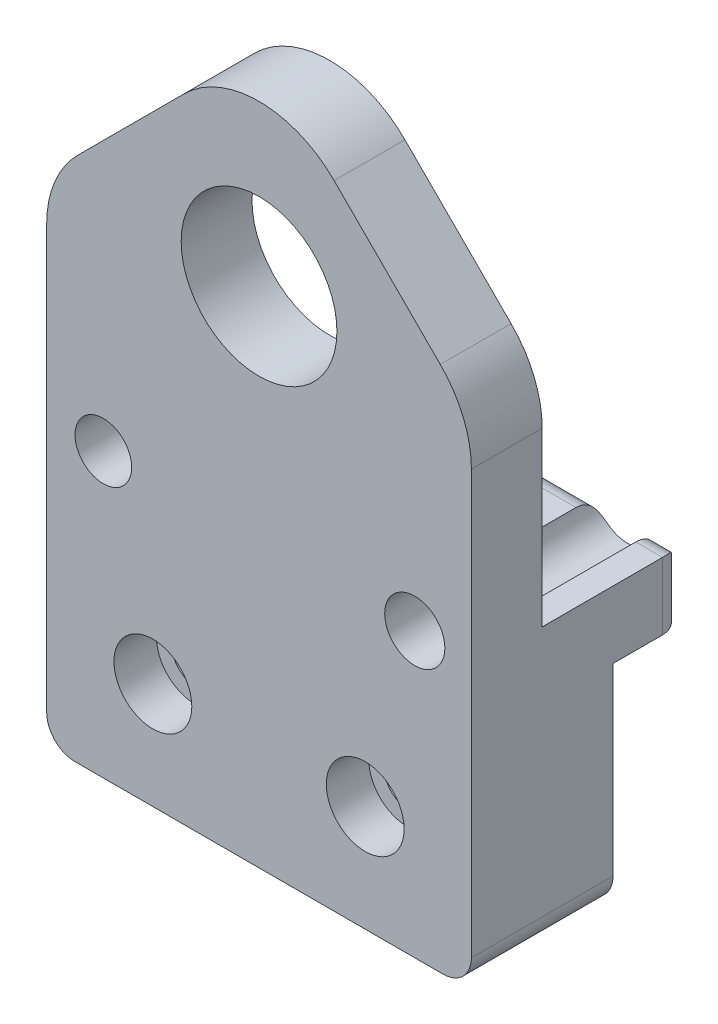
SolidWorks part; units mm, degrees
ref_plane "Front Plane" through (0, 0, 0) normal (0, 0, 1) x (1, 0, 0)
ref_plane "Top Plane" through (0, 0, 0) normal (0, 1, 0) x (1, 0, 0)
ref_plane "Right Plane" through (0, 0, 0) normal (1, 0, 0) x (0, 0, -1)
sketch "Esboço2" plane through (0, 0, 0) normal (0, 0, 1) x (1, 0, 0)
  line L0 (250, 102.2122) -> (250, 76.2122) construction
  line L1 (190, 102.2122) -> (190, 76.2122) construction
  line L2 (250, 102.2122) -> (250, 76.2122)
  line L3 (190, 102.2122) -> (190, 76.2122)
  line L4 (194, 72.2122) -> (246, 72.2122)
  line L6 (194, 172.2122) -> (246, 172.2122) construction
  line L14 (209.3934, 161.6056) -> (194.3934, 146.6056)
  line L15 (190, 76.2122) -> (190, 168.2122) construction
  line L16 (190, 135.999) -> (190, 102.2122)
  line L17 (230.6066, 161.6056) -> (245.6066, 146.6056)
  line L18 (250, 168.2122) -> (250, 76.2122) construction
  line L19 (250, 135.999) -> (250, 102.2122)
  arc A0 (190, 76.2122) -> (194, 72.2122) centre (194, 76.2122) ccw construction
  arc A1 (246, 72.2122) -> (250, 76.2122) centre (246, 76.2122) ccw construction
  arc A2 (190, 76.2122) -> (194, 72.2122) centre (194, 76.2122) ccw
  arc A3 (246, 72.2122) -> (250, 76.2122) centre (246, 76.2122) ccw
  circle A13 centre (198, 112.2122) radius 4
  circle A14 centre (198, 112.2122) radius 4
  circle A16 centre (242, 112.2122) radius 4.25
  circle A17 centre (242, 112.2122) radius 4.25
  arc A18 (209.3934, 161.6056) -> (230.6066, 161.6056) centre (220, 150.999) cw
  arc A19 (245.6066, 146.6056) -> (250, 135.999) centre (235, 135.999) cw
  circle A20 centre (220, 143.3622) radius 11
  arc A21 (194.3934, 146.6056) -> (190, 135.999) centre (205, 135.999) ccw
  point P15 (220, 172.2122)
  point P21 (220, 172.2122)
  point P29 (250, 142.2122)
  point P32 (190, 142.2122)
  dimension "D3" = 22
  dimension "D4" = 15
  dimension "D5" = 15
  dimension "D1" = 0
  dimension "D2" = 0
extrude "Ressalto-extrusão1" add sketch "Esboço2" along normal blind 20
sketch "Esboço3" plane through (0, 0, 0) normal (0, 0, -1) x (-1, 0, 0)
  line L0 (-440, 102.2122) -> (0, 102.2122) construction
  line L1 (-440, 102.2122) -> (0, 102.2122)
  line L2 (-190, 135.999) -> (-190, 76.2122) construction
  line L4 (-190, 102.2122) -> (-250, 102.2122)
  line L5 (-190, 102.2122) -> (-190, 111.6979)
  line L6 (-190, 111.6979) -> (-194.0332, 111.6979)
  line L7 (-250, 102.2122) -> (-250, 111.6979)
  line L8 (-250, 76.2122) -> (-250, 135.999) construction
  line L9 (-190, 111.6979) -> (-250, 111.6979) construction
  line L10 (-246.2188, 111.6979) -> (-250, 111.6979)
  line L11 (-201.9668, 111.6979) -> (-237.7812, 111.6979)
  circle A2 centre (-242, 112.2122) radius 4.25
  arc A3 (-246.2188, 111.6979) -> (-237.7812, 111.6979) centre (-242, 112.2122) ccw
  circle A5 centre (-198, 112.2122) radius 4
  arc A6 (-201.9668, 111.6979) -> (-194.0332, 111.6979) centre (-198, 112.2122) ccw
  line M4 (-190, 76.2122) -> (-190, 135.999)
  line M10 (-250, 135.999) -> (-250, 76.2122)
  circle M11 centre (-242, 112.2122) radius 4.25
  circle M13 centre (-198, 112.2122) radius 4
  dimension "D1" = 0
  dimension "D2" = 0
extrude "Ressalto-extrusão2" add sketch "Esboço3" along normal blind 10 contours L11 L10 L1 L6 M13 M11 M10 M4
fillet "Filete1" radius 3 5 edges at (192.0166, 111.6979, -10) (248.1094, 111.6979, -10) (219.874, 111.6979, -10) (250, 106.955, -10) (190, 106.955, -10)
sketch "Esboço4" plane through (0, 0, 0) normal (0, 0, -1) x (-1, 0, 0)
  line L14 (-194.0332, 111.6979) -> (-190, 111.6979)
  line L15 (-190, 111.6979) -> (-190, 135.999)
  line L16 (-194.3934, 146.6056) -> (-209.3934, 161.6056)
  line L17 (-230.6066, 161.6056) -> (-245.6066, 146.6056)
  line L18 (-250, 135.999) -> (-250, 111.6979)
  line L19 (-250, 111.6979) -> (-246.2188, 111.6979)
  line L20 (-237.7812, 111.6979) -> (-201.9668, 111.6979)
  line L21 (-194.0332, 111.6979) -> (-190, 111.6979)
  line L22 (-190, 111.6979) -> (-190, 135.999)
  line L23 (-194.3934, 146.6056) -> (-209.3934, 161.6056)
  line L24 (-230.6066, 161.6056) -> (-245.6066, 146.6056)
  line L25 (-250, 135.999) -> (-250, 111.6979)
  line L26 (-250, 111.6979) -> (-246.2188, 111.6979)
  line L27 (-237.7812, 111.6979) -> (-201.9668, 111.6979)
  arc A10 (-190, 135.999) -> (-194.3934, 146.6056) centre (-205, 135.999) ccw
  arc A11 (-209.3934, 161.6056) -> (-230.6066, 161.6056) centre (-220, 150.999) ccw
  arc A12 (-245.6066, 146.6056) -> (-250, 135.999) centre (-235, 135.999) ccw
  arc A13 (-237.7812, 111.6979) -> (-246.2188, 111.6979) centre (-242, 112.2122) ccw
  arc A14 (-194.0332, 111.6979) -> (-201.9668, 111.6979) centre (-198, 112.2122) ccw
  arc A15 (-190, 135.999) -> (-194.3934, 146.6056) centre (-205, 135.999) ccw
  arc A16 (-209.3934, 161.6056) -> (-230.6066, 161.6056) centre (-220, 150.999) ccw
  arc A17 (-245.6066, 146.6056) -> (-250, 135.999) centre (-235, 135.999) ccw
  arc A18 (-237.7812, 111.6979) -> (-246.2188, 111.6979) centre (-242, 112.2122) ccw
  arc A19 (-194.0332, 111.6979) -> (-201.9668, 111.6979) centre (-198, 112.2122) ccw
  dimension "D1" = 0
extrude "Corte-extrusão1" cut sketch "Esboço4" against normal blind 10
sketch "Esboço7" plane through (0, 0, 20) normal (0, 0, 1) x (1, 0, 0)
  circle A2 centre (235, 87.2122) radius 5.5
  circle A3 centre (235, 87.2122) radius 5.5 construction
  circle A5 centre (205, 87.2122) radius 5.5
  circle A6 centre (205, 87.2122) radius 5.5 construction
  dimension "D1" = 0
  dimension "D2" = 0
hole_wizard "Rebaixo para SHCS M61" positions "Esboço8" profile "Esboço9" counterbore size "M6" standard "Ansi Metric" end condition through all
sketch "Esboço8" plane through (0, 0, 20) normal (0, 0, 1) x (1, 0, 0)
  point P0 (235, 87.2122)
  point P3 (205, 87.2122)
sketch "Esboço9" plane through (235, 87.2122, 20) normal (1, 0, 0) x (0, -1, 0)
  line L0 (0, 0) -> (0, 30)
  line L1 (0, 30) -> (3.3, 30)
  line L3 (3.3, 30) -> (3.3, 6)
  line L4 (3.3, 6) -> (5.5, 6)
  line L5 (5.5, 6) -> (5.5, 0)
  line L7 (5.5, 0) -> (0, 0)
  line L11 (0, -6.35) -> (0, 107.95) construction
  dimension "Thru Hole Dia." = 6.6
  dimension "Thru Hole Depth" = 30
  dimension "C'Bore Dia." = 11
  dimension "C'Bore Depth" = 6
